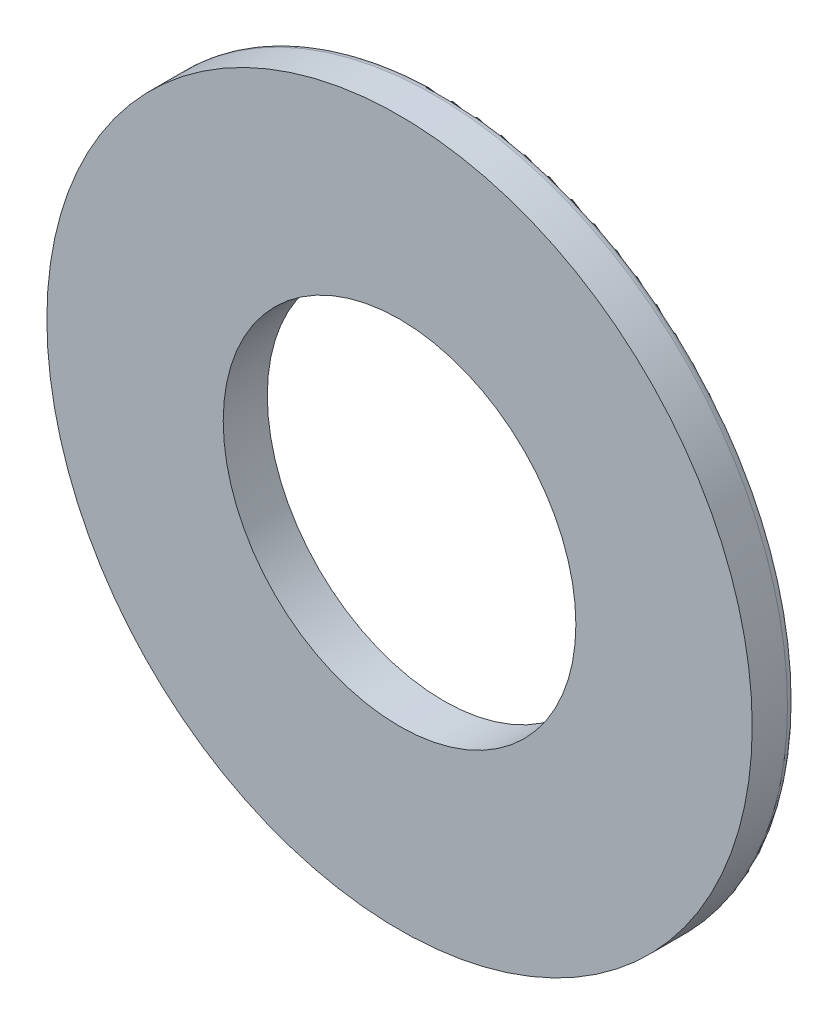
SolidWorks part; units mm, degrees
ref_plane "Plan de face" through (0, 0, 0) normal (0, 0, 1) x (1, 0, 0)
ref_plane "Plan de dessus" through (0, 0, 0) normal (0, 1, 0) x (1, 0, 0)
ref_plane "Plan de droite" through (0, 0, 0) normal (1, 0, 0) x (0, 0, -1)
sketch "Esquisse1" plane through (0, 0, 0) normal (0, 0, 1) x (1, 0, 0)
  circle A0 centre (0, 0) radius 1
  circle A1 centre (0, 0) radius 2
  dimension "D1" = 4
  dimension "D2" = 2
extrude "Boss.-Extru.1" add sketch "Esquisse1" along normal blind 0.25
fillet "Congé1" radius 0.05 1 edges at (2, 0, 0)
